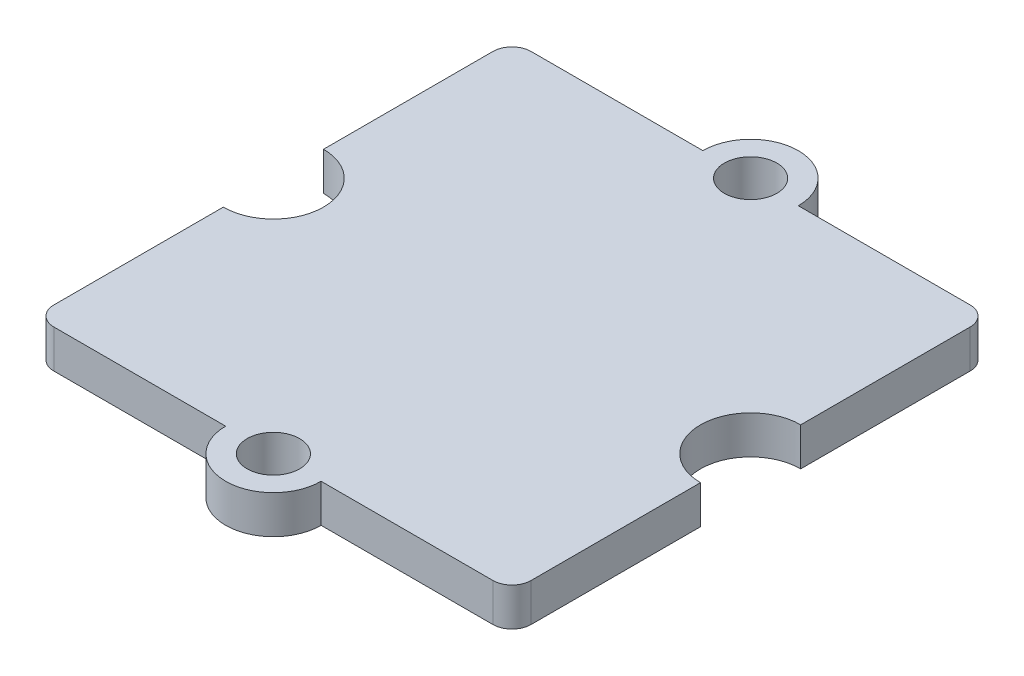
SolidWorks part; units mm, degrees
ref_plane "Plan de face" through (0, 0, 0) normal (0, 0, 1) x (1, 0, 0)
ref_plane "Plan de dessus" through (0, 0, 0) normal (0, 1, 0) x (1, 0, 0)
ref_plane "Plan de droite" through (0, 0, 0) normal (1, 0, 0) x (0, 0, -1)
sketch "Esquisse1" plane through (0, 0, 0) normal (0, 1, 0) x (1, 0, 0)
  line L1 (-9.2, -10) -> (9.2, -10)
  line L2 (-10, -9.2) -> (-10, 9.2)
  line L3 (-9.2, 10) -> (9.2, 10)
  line L4 (10, -9.2) -> (10, 9.2)
  line L5 (-10, -10) -> (10, 10) construction
  line L6 (-10, 10) -> (10, -10) construction
  circle A0 centre (0, 10) radius 2
  circle A1 centre (0, -10) radius 2
  circle A2 centre (-10, 0) radius 2.1
  circle A3 centre (10, 0) radius 2.1
  circle A4 centre (0, 10) radius 1.1
  arc A5 (9.2, 10) -> (10, 9.2) centre (9.2, 9.2) cw
  circle A6 centre (0, -10) radius 1.1
  arc A7 (-9.2, -10) -> (-10, -9.2) centre (-9.2, -9.2) cw
  arc A8 (9.2, -10) -> (10, -9.2) centre (9.2, -9.2) ccw
  arc A9 (-10, 9.2) -> (-9.2, 10) centre (-9.2, 9.2) cw
  point P0 (0, 0)
  dimension "D2" = 0.8
  dimension "D3" = 4.2
  dimension "D4" = 2.2
  dimension "D5" = 4
  dimension "D1" = 20
extrude "Boss.-Extru.1" add sketch "Esquisse1" along normal mid plane 1.6 contours A9 L2 A2 A7 L1 A1 A8 L4 A3 A5 L3 A0 | A4 L3 A0 | A4 L3 A0 | A6 L1 A1 | A6 L1 A1
